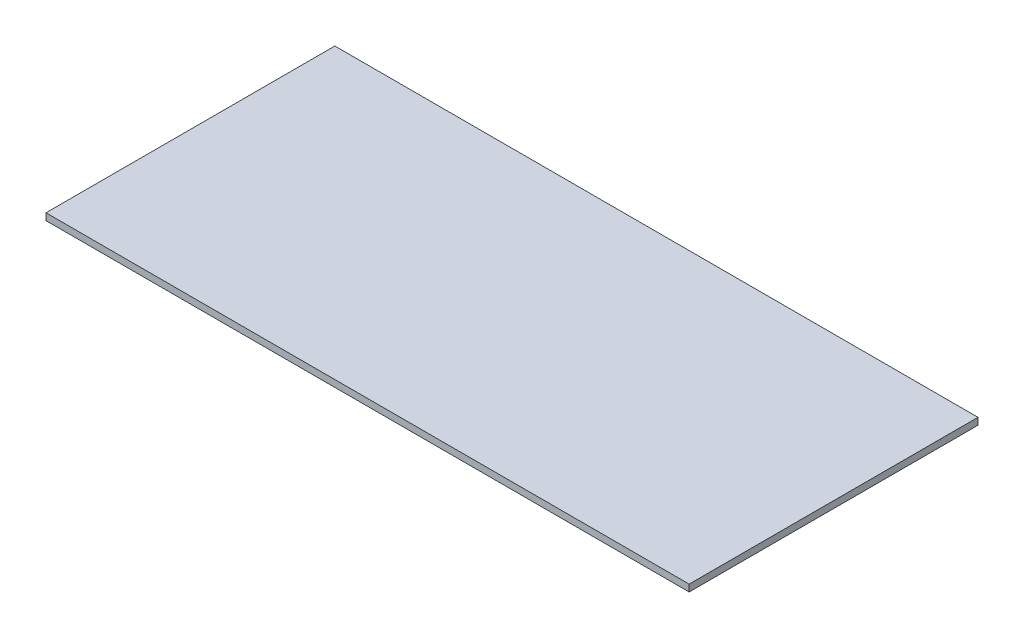
SolidWorks part; units mm, degrees
ref_plane "Front Plane" through (0, 0, 0) normal (0, 0, 1) x (1, 0, 0)
ref_plane "Top Plane" through (0, 0, 0) normal (0, 1, 0) x (1, 0, 0)
ref_plane "Right Plane" through (0, 0, 0) normal (1, 0, 0) x (0, 0, -1)
sketch "Sketch1" plane through (0, 0, 0) normal (0, 1, 0) x (1, 0, 0)
  line L1 (-119.4817, 53.6595) -> (119.4817, 53.6595)
  line L2 (-119.4817, 53.6595) -> (-119.4817, -53.6595)
  line L3 (-119.4817, -53.6595) -> (119.4817, -53.6595)
  line L4 (119.4817, 53.6595) -> (119.4817, -53.6595)
  line L5 (-119.4817, 53.6595) -> (119.4817, -53.6595) construction
  line L6 (-119.4817, -53.6595) -> (119.4817, 53.6595) construction
  point P0 (0, 0)
extrude "Boss-Extrude1" add sketch "Sketch1" along normal blind 2.54
